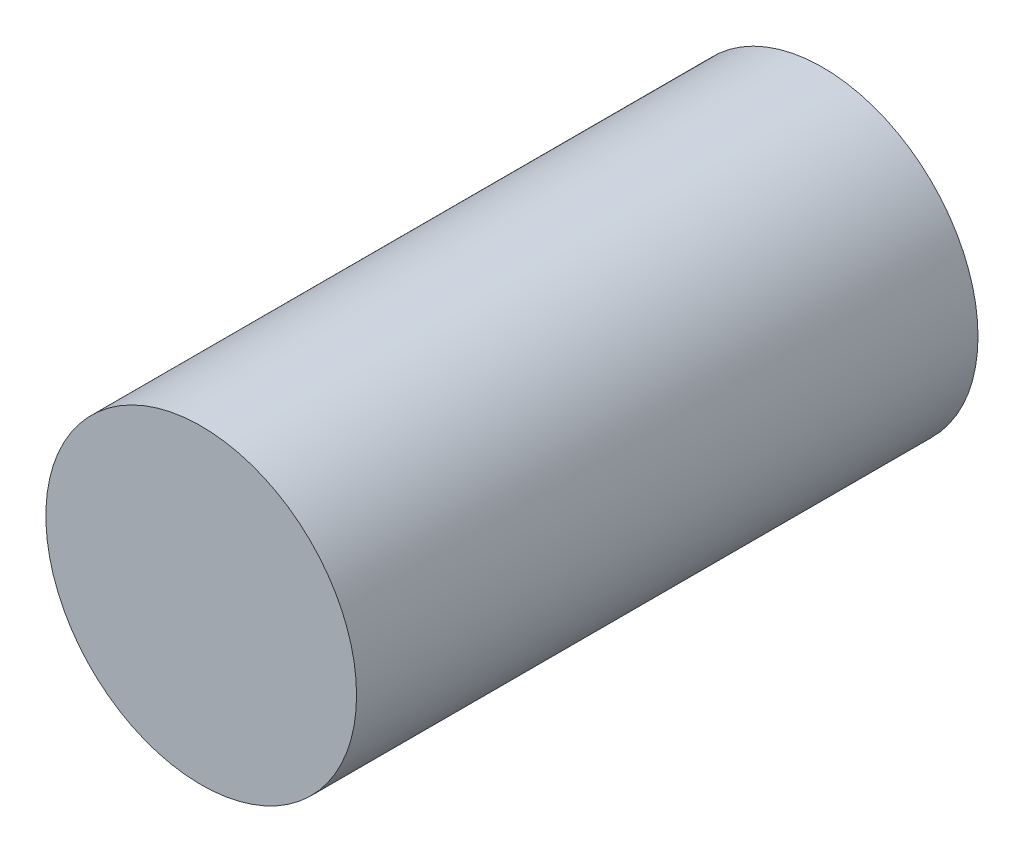
SolidWorks part; units mm, degrees
ref_plane "Alzado" through (0, 0, 0) normal (0, 0, 1) x (1, 0, 0)
ref_plane "Planta" through (0, 0, 0) normal (0, 1, 0) x (1, 0, 0)
ref_plane "Vista lateral" through (0, 0, 0) normal (1, 0, 0) x (0, 0, -1)
sketch "Croquis1" plane through (0, 0, 0) normal (0, 0, 1) x (1, 0, 0)
  circle A0 centre (0, 0) radius 0.25
  dimension "D1" = 0.5
extrude "Saliente-Extruir1" add sketch "Croquis1" along normal blind 1
